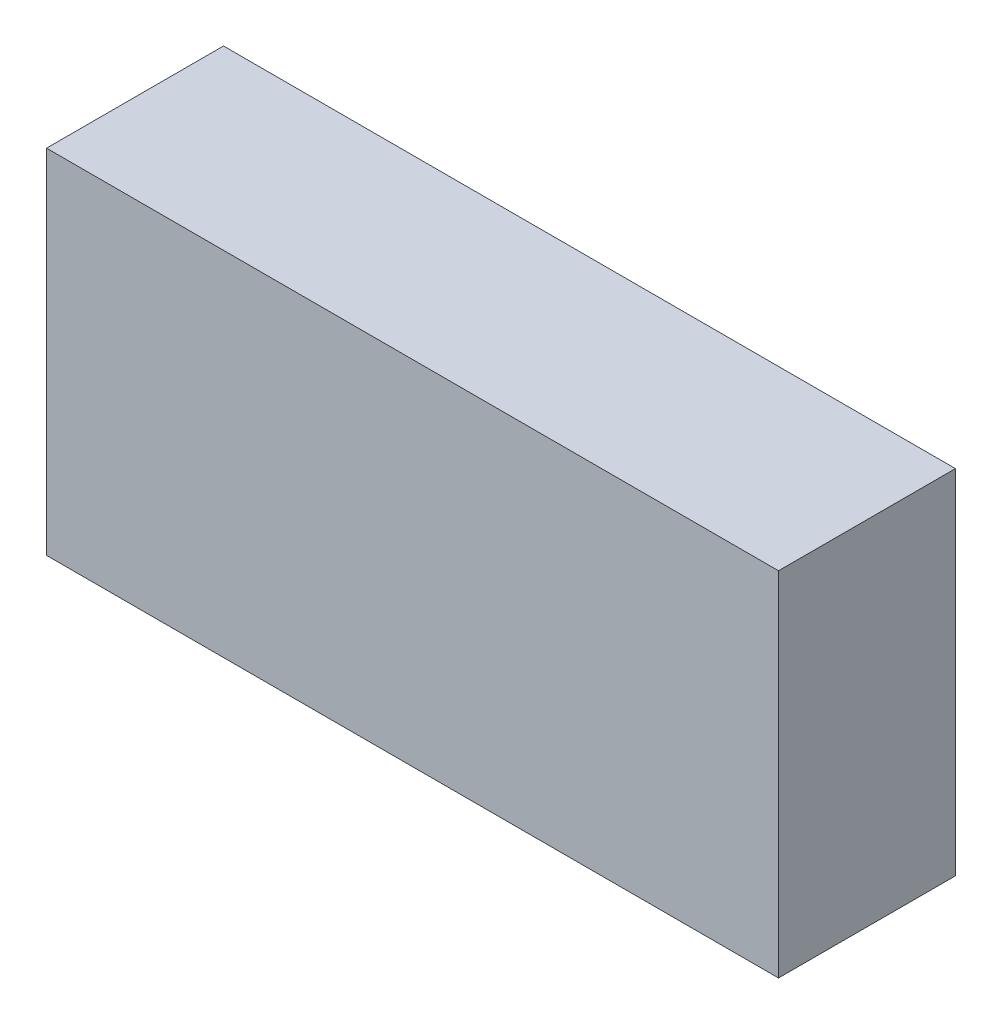
SolidWorks part; units mm, degrees
ref_plane "Front Plane" through (0, 0, 0) normal (0, 0, 1) x (1, 0, 0)
ref_plane "Top Plane" through (0, 0, 0) normal (0, 1, 0) x (1, 0, 0)
ref_plane "Right Plane" through (0, 0, 0) normal (1, 0, 0) x (0, 0, -1)
sketch "Sketch1" plane through (0, 0, 0) normal (0, 0, 1) x (1, 0, 0)
  line L1 (0, 0) -> (202, 0)
  line L2 (0, 0) -> (0, 97.33)
  line L3 (0, 97.33) -> (202, 97.33)
  line L4 (202, 0) -> (202, 97.33)
  dimension "D1" = 202
  dimension "D2" = 97.33
extrude "Boss-Extrude1" add sketch "Sketch1" along normal blind 48.83
